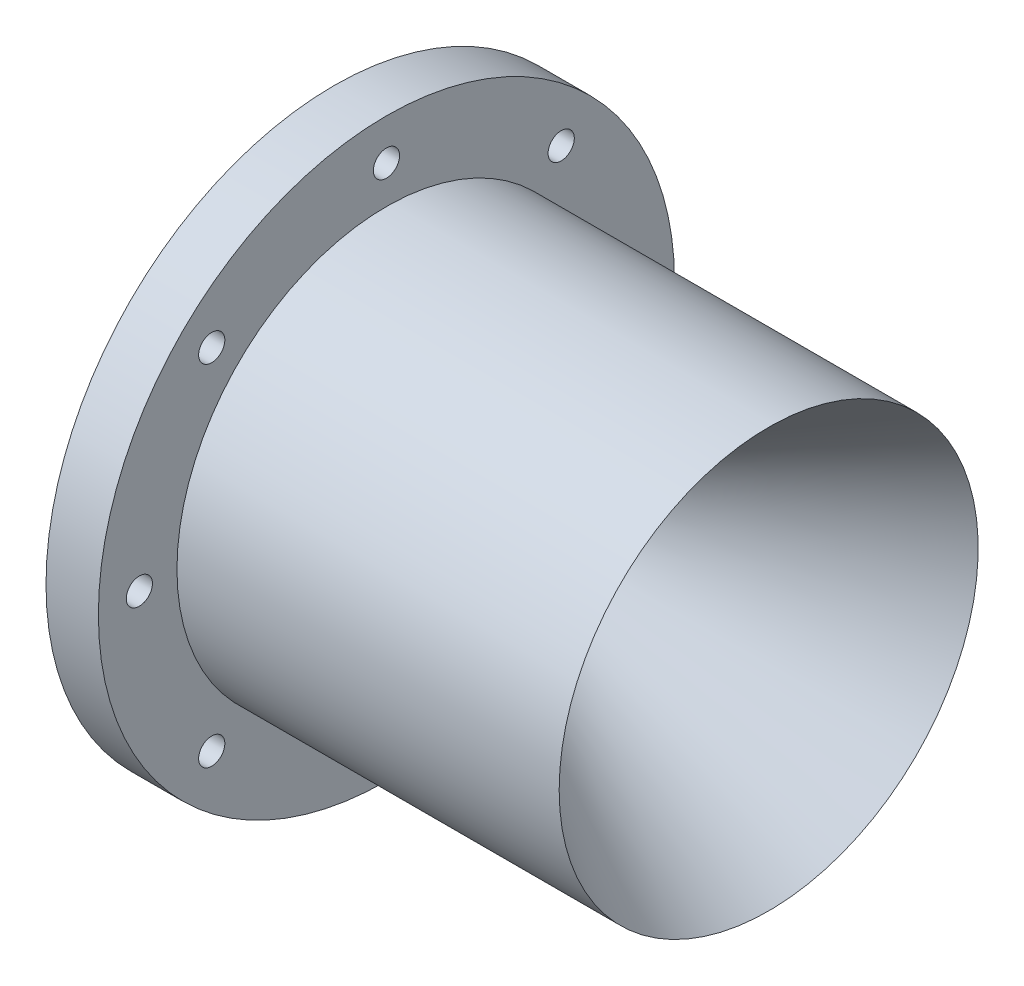
SolidWorks part; units mm, degrees
material "C (Graphite)"
ref_plane "Front Plane" through (0, 0, 0) normal (0, 0, 1) x (1, 0, 0)
ref_plane "Top Plane" through (0, 0, 0) normal (0, 1, 0) x (1, 0, 0)
ref_plane "Right Plane" through (0, 0, 0) normal (1, 0, 0) x (0, 0, -1)
sketch "Sketch1" plane through (0, 0, 0) normal (0, 0, 1) x (1, 0, 0)
  line L0 (0, 0) -> (215.3765, 0) construction
  line L1 (0, 0) -> (0, 93.6004) construction
  line L3 (0, 7.9375) -> (72.3242, 50.8)
  line L10 (0, 7.9375) -> (-12.7, 7.9375)
  line L22 (-12.7, 7.9375) -> (-33.0473, 41.275)
  line L23 (-33.0473, 50.8) -> (-33.0473, 41.275)
  line L24 (-33.0473, 50.8) -> (-33.0473, 69.85)
  line L25 (-33.0473, 69.85) -> (-20.3473, 69.85)
  line L26 (-20.3473, 69.85) -> (-20.3473, 50.8)
  line L27 (-20.3473, 50.8) -> (72.3242, 50.8)
  dimension "D3" = 7.9375
  dimension "D4" = 9.525
  dimension "D7" = 12.7
  dimension "D10" = 50.8
  dimension "D11" = 19.05
  dimension "D12" = 12.7
revolve "Revolve1" add sketch "Sketch1" angle 360 about L0
sketch "Sketch2" plane through (-33.0473, 0, 0) normal (-1, 0, 0) x (0, 0, 1)
  circle A0 centre (0, 0) radius 47.625
  circle A1 centre (0, 0) radius 49.53
  dimension "D1" = 99.06
  dimension "D2" = 95.25
extrude "Cut-Extrude1" cut sketch "Sketch2" against normal blind 1.1176
sketch "Sketch3" plane through (-33.0473, 0, 0) normal (-1, 0, 0) x (0, 0, 1)
  circle A0 centre (0, 59.9186) radius 3.175
  circle A1 centre (42.3688, 42.3688) radius 3.175
  circle A2 centre (59.9186, 0) radius 3.175
  circle A3 centre (42.3688, -42.3688) radius 3.175
  circle A4 centre (0, -59.9186) radius 3.175
  circle A5 centre (-42.3688, -42.3688) radius 3.175
  circle A6 centre (-59.9186, 0) radius 3.175
  circle A7 centre (-42.3688, 42.3688) radius 3.175
  point P36 (0, 0)
  dimension "D1" = 6.35
  dimension "D2" = 59.9186
  dimension "D3" = 8
extrude "Cut-Extrude2" cut sketch "Sketch3" against normal up to next
